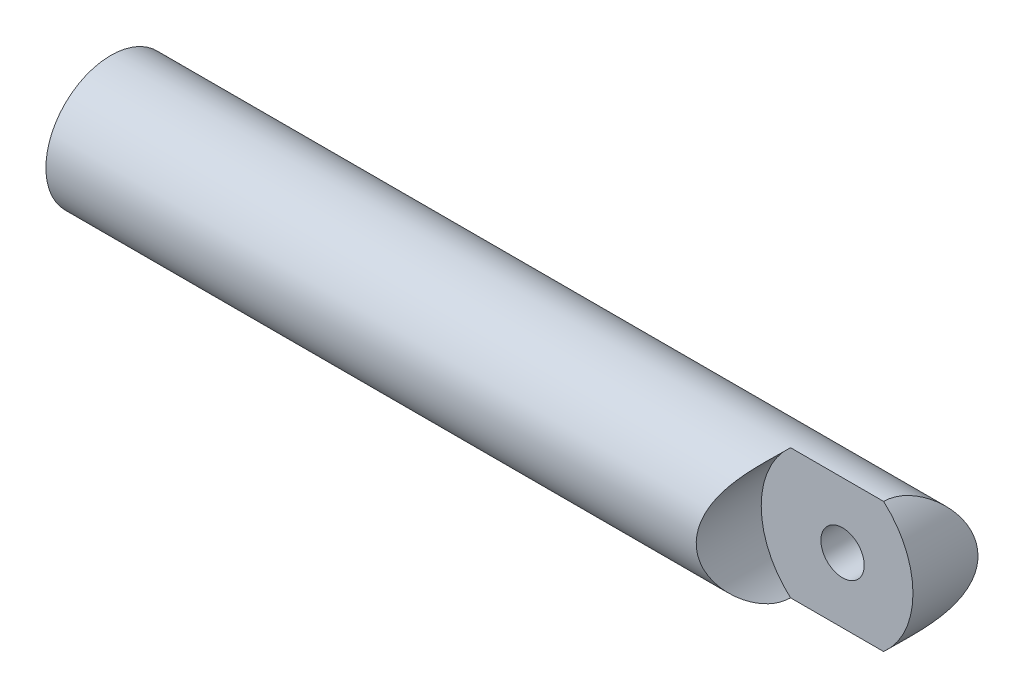
SolidWorks part; units mm, degrees
material "AISI 1035 Steel (SS)"
ref_plane "Front Plane" through (0, 0, 0) normal (0, 0, 1) x (1, 0, 0)
ref_plane "Top Plane" through (0, 0, 0) normal (0, 1, 0) x (1, 0, 0)
ref_plane "Right Plane" through (0, 0, 0) normal (1, 0, 0) x (0, 0, -1)
sketch "Sketch1" plane through (0, 0, 0) normal (1, 0, 0) x (0, 0, -1)
  circle A0 centre (0, 0) radius 4.7041
extrude "Boss-Extrude1" add sketch "Sketch1" against normal blind 58.0238
sketch "Sketch2" plane through (0, 0, 0) normal (0, 0, 1) x (1, 0, 0)
  line L0 (-6.2738, 6.2738) -> (2.931, 6.2738)
  line L1 (2.931, 6.2738) -> (2.931, -6.2738)
  line L2 (2.931, -6.2738) -> (-6.2738, -6.2738)
  line L3 (-58.0238, 4.7041) -> (-58.0238, -4.7041) construction
  arc A0 (-6.2738, -6.2738) -> (-6.2738, 6.2738) centre (-6.2738, 0) ccw
  dimension "D1" = 51.75
extrude "Cut-Extrude1" cut sketch "Sketch2" against normal through all and the other way through all
sketch "Sketch3" plane through (0, 0, 0) normal (0, 0, 1) x (1, 0, 0)
  line L0 (-58.0238, 4.7041) -> (-58.0238, -4.7041) construction
  circle A0 centre (-4.7041, 0) radius 6.2738
  dimension "D1" = 53.3197
extrude "Cut-Extrude2" cut sketch "Sketch3" along normal through all
sketch "Sketch4" plane through (0, 0, 0) normal (0, 0, 1) x (1, 0, 0)
  line L0 (-58.0238, 4.7041) -> (-58.0238, -4.7041) construction
  circle A0 centre (-5.0952, 0) radius 1.5672
  dimension "D1" = 52.9285
  dimension "D2" = 3.1344
extrude "Cut-Extrude3" cut sketch "Sketch4" against normal through all
